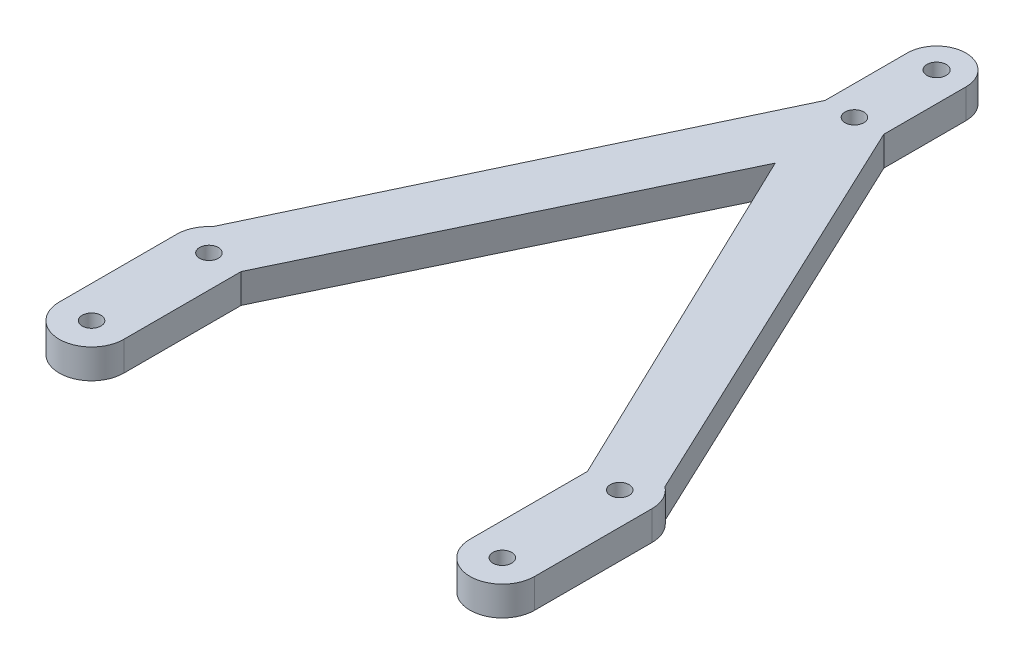
SolidWorks part; units mm, degrees
ref_plane "前视基准面" through (0, 0, 0) normal (0, 0, 1) x (1, 0, 0)
ref_plane "上视基准面" through (0, 0, 0) normal (0, 1, 0) x (1, 0, 0)
ref_plane "右视基准面" through (0, 0, 0) normal (1, 0, 0) x (0, 0, -1)
sketch "草图1" plane through (0, 0, 0) normal (0, 1, 0) x (1, 0, 0)
  line L0 (0, 10.1204) -> (0, -9.4519) construction
  line L1 (-35, -21.6581) -> (-35, 11.7885) construction
  line L2 (-29.5, 11.7885) -> (-29.5, -8.2115)
  line L3 (-40.5, 11.7885) -> (-40.5, -8.2115)
  line L4 (-35, 11.7885) -> (35, 11.7885) construction
  line L5 (-35, -8.2115) -> (35, -8.2115) construction
  line L8 (40.5, 11.7885) -> (40.5, -8.2115)
  line L9 (29.5, 11.7885) -> (29.5, -8.2115)
  line L14 (0, 9.5094) -> (0, 137.0676) construction
  line L15 (-5, 100.7885) -> (-5, 86.7885)
  line L16 (5, 100.7885) -> (5, 86.7885)
  line L17 (-5, 86.7885) -> (-38.553, 15.9869)
  line L20 (38.3481, 16.152) -> (5, 86.7885)
  line L21 (-29.5, 11.7885) -> (0, 73.2885)
  line L22 (0, 73.2885) -> (29.5, 11.7885)
  circle A0 centre (-35, -8.2115) radius 1.6
  circle A1 centre (-35, 11.7885) radius 1.6
  circle A2 centre (35, 11.7885) radius 1.6
  circle A3 centre (35, -8.2115) radius 1.6
  arc A6 (-40.5, -8.2115) -> (-29.5, -8.2115) centre (-35, -8.2115) ccw
  arc A7 (-38.553, 15.9869) -> (-40.5, 11.7885) centre (-35, 11.7885) ccw
  arc A10 (40.5, -8.2115) -> (29.5, -8.2115) centre (35, -8.2115) cw
  arc A11 (38.3481, 16.152) -> (40.5, 11.7885) centre (35, 11.7885) cw
  circle A12 centre (0, 100.7885) radius 1.6348
  circle A13 centre (0, 86.7885) radius 1.6
  arc A14 (5, 100.7885) -> (-5, 100.7885) centre (0, 100.7885) ccw
  point P24 (0, 63.2885)
  point P34 (0, 73.2885)
  dimension "D1" = 3.2
  dimension "D2" = 3.2
  dimension "D4" = 75
  dimension "D6" = 14
  dimension "D3" = 35
  dimension "D5" = 20
  dimension "3" = 5.5
extrude "凸台-拉伸1" add sketch "草图1" along normal blind 5
